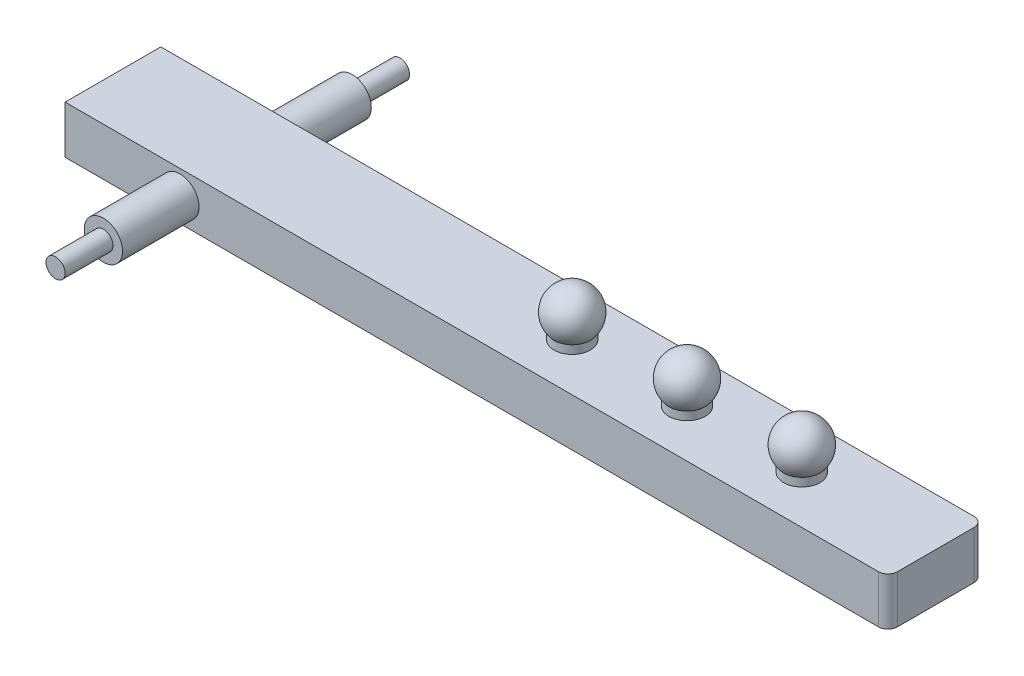
SolidWorks part; units mm, degrees
ref_plane "前视基准面" through (0, 0, 0) normal (0, 0, 1) x (1, 0, 0)
ref_plane "上视基准面" through (0, 0, 0) normal (0, 1, 0) x (1, 0, 0)
ref_plane "右视基准面" through (0, 0, 0) normal (1, 0, 0) x (0, 0, -1)
sketch "草图1" plane through (0, 0, 0) normal (0, 0, 1) x (1, 0, 0)
  circle A0 centre (0, 0) radius 20
  dimension "D1" = 40
extrude "凸台-拉伸1" add sketch "草图1" along normal mid plane 260
sketch "草图2" plane through (0, 0, 0) normal (0, 0, 1) x (1, 0, 0)
  line L0 (-120, 0) -> (360, 0) construction
  line L1 (360, 0) -> (480, 0) construction
  line L2 (480, 0) -> (720, 0) construction
  line L3 (720, 0) -> (600, 0) construction
  line L4 (720, 0) -> (740, 0) construction
  line L10 (-120, 25) -> (740, 25)
  line L11 (-120, 25) -> (-120, -25)
  line L12 (-120, -25) -> (740, -25)
  line L13 (740, 25) -> (740, -25)
  dimension "D1" = 120
  dimension "D2" = 360
  dimension "D3" = 120
  dimension "D4" = 120
  dimension "D5" = 120
  dimension "D6" = 20
  dimension "D7" = 50
extrude "凸台-拉伸2" add sketch "草图2" along normal mid plane 100
sketch "草图3" plane through (0, 0, 130) normal (0, 0, 1) x (1, 0, 0)
  circle A0 centre (0, 0) radius 10
extrude "凸台-拉伸3" add sketch "草图3" along normal blind 50
mirror "镜向1" about plane through (0, 0, 0) normal (0, 0, 1) of "凸台-拉伸3"
sketch "草图6" plane through (0, 0, 0) normal (0, 0, 1) x (1, 0, 0)
  line L0 (360, 25) -> (360, 124.3293) construction
  line L1 (740, 25) -> (-120, 25) construction
  line L2 (360, 75) -> (360, 50)
  line L4 (360, 50) -> (360, 25)
  line L5 (360, 25) -> (378.9937, 25)
  line L6 (378.9937, 33.7445) -> (378.9937, 25)
  line L7 (0, -55) -> (0, 55) construction
  arc A0 (378.9937, 33.7445) -> (360, 75) centre (360, 50) ccw
  dimension "D1" = 50
  dimension "D2" = 25
  dimension "D3" = 360
revolve "旋转3" add sketch "草图6" angle 360 about L0
pattern_linear "阵列(线性)16" count 3 spacing 120 along (1, 0, 0) of "旋转3"
fillet "圆角1" radius 10 2 edges at (740, 0, -50) (740, 0, 50)
